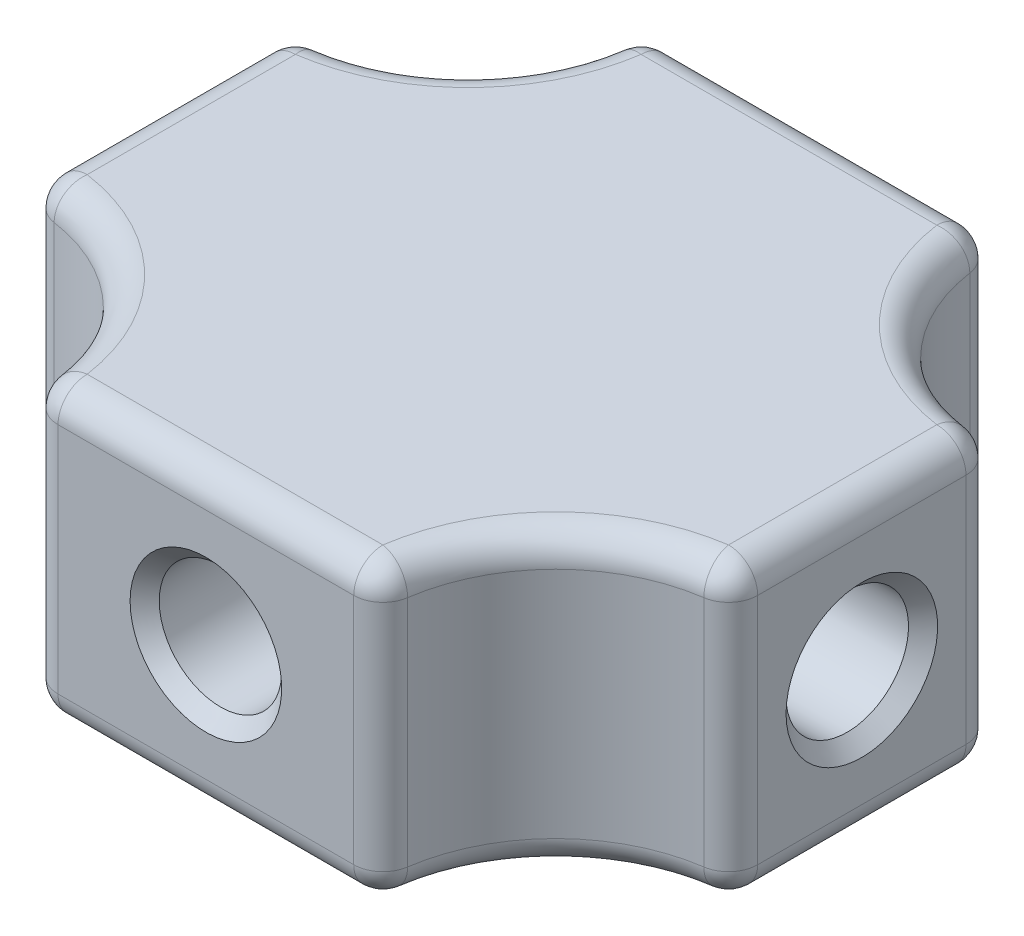
SolidWorks part; units mm, degrees
ref_plane "Vorne" through (0, 0, 0) normal (0, 0, 1) x (1, 0, 0)
ref_plane "Oben" through (0, 0, 0) normal (0, 1, 0) x (1, 0, 0)
ref_plane "Rechts" through (0, 0, 0) normal (1, 0, 0) x (0, 0, -1)
sketch "Skizze1" plane through (0, 0, 0) normal (0, 1, 0) x (1, 0, 0)
  line L0 (0, -55) -> (0, 55) construction
  line L1 (-12, 10.5) -> (12, 10.5)
  line L2 (-12, 10.5) -> (-12, -10.5)
  line L3 (-12, -10.5) -> (12, -10.5)
  line L4 (12, 10.5) -> (12, -10.5)
  line L5 (-55, 0) -> (55, 0) construction
  dimension "D1" = 21
  dimension "D2" = 24
  dimension "D3" = 12
  dimension "D4" = 10.5
extrude "Aufsatz-Linear austragen1" add sketch "Skizze1" along normal blind 10
sketch "Skizze2" plane through (0, 0, 0) normal (1, 0, 0) x (0, 0, -1)
  line L0 (11.55, 0) -> (-11.55, 0) construction
  line L1 (0, 5.5) -> (0, -5.5) construction
  circle A0 centre (0, 5) radius 2.1
  dimension "D1" = 4.2
  dimension "D2" = 5
extrude "Schnitt-Linear austragen1" cut sketch "Skizze2" against normal blind 20 and the other way blind 20
sketch "Skizze3" plane through (0, 0, 0) normal (0, 0, 1) x (1, 0, 0)
  line L0 (11.55, 0) -> (-11.55, 0) construction
  line L1 (0, -5.5) -> (0, 5.5) construction
  circle A0 centre (0, 5) radius 2.1
  dimension "D1" = 4.2
  dimension "D2" = 5
extrude "Schnitt-Linear austragen2" cut sketch "Skizze3" against normal blind 20 and the other way blind 20
sketch "Skizze4" plane through (0, 10, 0) normal (0, 1, 0) x (-1, 0, 0)
  circle A0 centre (12, -10.5) radius 6
  circle A1 centre (-12, -10.5) radius 6
  circle A2 centre (-12, 10.5) radius 6
  circle A3 centre (12, 10.5) radius 6
  dimension "D1" = 12
extrude "Schnitt-Linear austragen3" cut sketch "Skizze4" against normal blind 10
fillet "Verrundung1" radius 1 8 edges at (12, 5, 4.5) (6, 5, 10.5) (-6, 5, 10.5) (-12, 5, 4.5) (-12, 5, -4.5) (-6, 5, -10.5) (6, 5, -10.5) (12, 5, -4.5)
fillet "Verrundung2" radius 1 32 edges at (-5.7265, 0, 10.2559) (0, 0, 10.5) (5.7265, 0, 10.2559) (7.7574, 0, 6.2574) (11.7559, 0, 4.2265) (12, 0, 0) (11.7559, 0, -4.2265) (7.7574, 0, -6.2574) (5.7265, 0, -10.2559) (0, 0, -10.5) (-5.7265, 0, -10.2559) (-7.7574, 0, -6.2574) (-11.7559, 0, -4.2265) (-12, 0, 0) (-11.7559, 0, 4.2265) (-5.7265, 10, 10.2559) (0, 10, 10.5) (5.7265, 10, 10.2559) (7.7574, 10, 6.2574) (11.7559, 10, 4.2265) (12, 10, 0) (11.7559, 10, -4.2265) (7.7574, 10, -6.2574) (5.7265, 10, -10.2559) (0, 10, -10.5) (-5.7265, 10, -10.2559) (-7.7574, 10, -6.2574) (-11.7559, 10, -4.2265) (-12, 10, 0) (-11.7559, 10, 4.2265) (-7.7574, 0, 6.2574) (-7.7574, 10, 6.2574)
chamfer "Fase1" distance 0.5 angle 45 4 edges at (12, 5, 2.1) (-2.1, 5, 10.5) (-12, 5, -2.1) (2.1, 5, -10.5)
